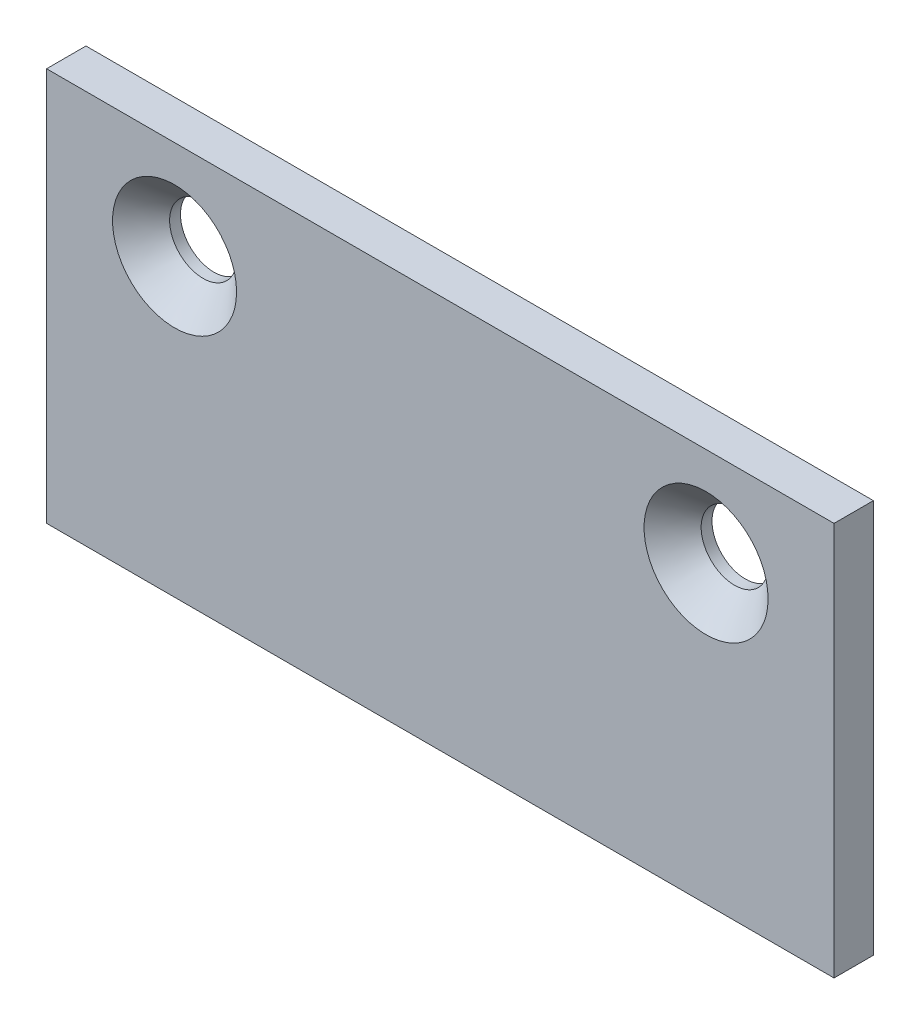
SolidWorks part; units mm, degrees
ref_plane "前基準面" through (0, 0, 0) normal (0, 0, 1) x (1, 0, 0)
ref_plane "上基準面" through (0, 0, 0) normal (0, 1, 0) x (1, 0, 0)
ref_plane "右基準面" through (0, 0, 0) normal (1, 0, 0) x (0, 0, -1)
sketch "草圖1" plane through (0, 0, 0) normal (0, 0, 1) x (1, 0, 0)
  line L0 (0, 10) -> (0, -10) construction
  line L1 (-20, 10) -> (20, 10)
  line L2 (-20, 10) -> (-20, -10)
  line L3 (-20, -10) -> (20, -10)
  line L4 (20, 10) -> (20, -10)
  dimension "D1" = 20
  dimension "D2" = 40
extrude "填料-伸長1" add sketch "草圖1" along normal blind 2
hole_wizard "M3 平錐坑頭螺釘的錐孔1" positions "草圖3" profile "草圖2" countersink size "M3" standard "JIS" end condition through all
sketch "草圖3" plane through (0, 0, 2) normal (0, 0, 1) x (1, 0, 0)
  line L0 (0, 10) -> (0, -10) construction
  line L1 (20, 10) -> (-20, 10) construction
  line L2 (-20, -10) -> (20, -10) construction
  line L4 (-20, 10) -> (-20, -10) construction
  point P0 (-13.5, 5)
  point P11 (13.5, 5)
  dimension "D1" = 5
  dimension "D2" = 6.5
sketch "草圖2" plane through (-13.5, 5, 2) normal (1, 0, 0) x (0, -1, 0)
  line L0 (0, 0) -> (0, 2)
  line L1 (0, 2) -> (1.7, 2)
  line L2 (1.7, 2) -> (1.7, 1.45)
  line L3 (1.7, 1.45) -> (3.15, 0)
  line L5 (3.15, 0) -> (0, 0)
  line L6 (-1.7, 1.45) -> (-3.15, 0) construction
  line L11 (0, -6.35) -> (0, 107.95) construction
  dimension "貫穿孔直徑" = 3.4
  dimension "貫穿孔深度" = 2
  dimension "近端錐孔直徑" = 6.3
  dimension "近端錐孔角度" = 90
